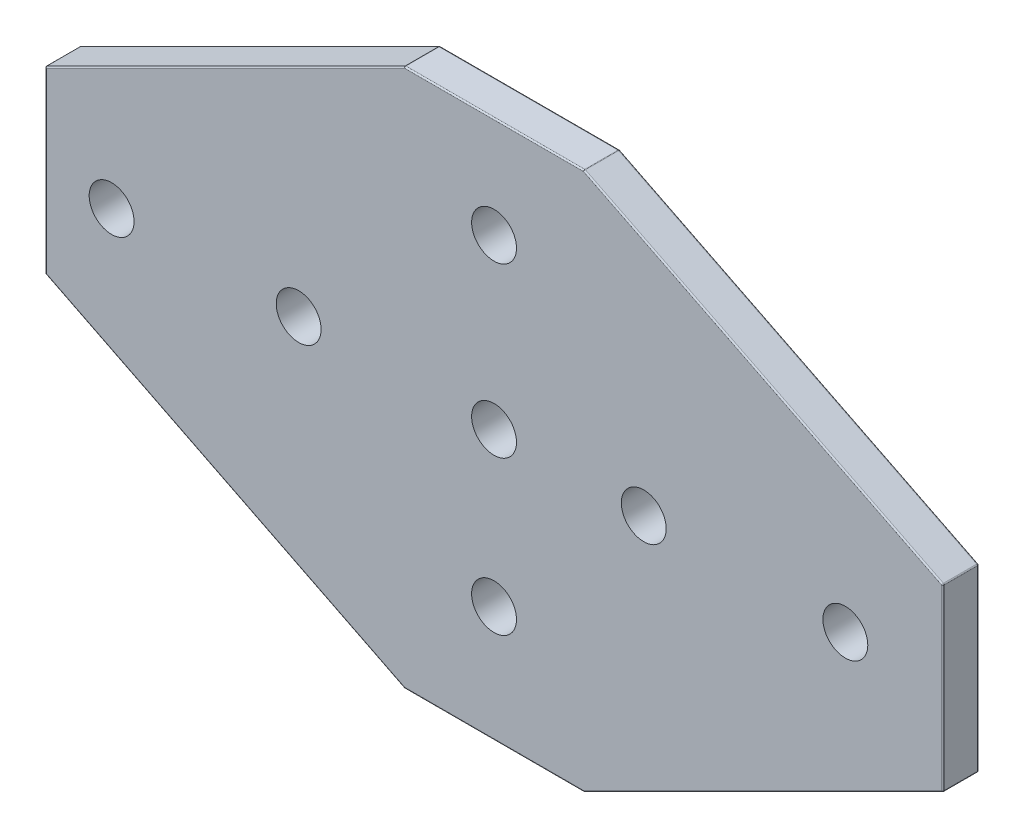
SolidWorks part; units mm, degrees
ref_plane "Front Plane" through (0, 0, 0) normal (0, 0, 1) x (1, 0, 0)
ref_plane "Top Plane" through (0, 0, 0) normal (0, 1, 0) x (1, 0, 0)
ref_plane "Right Plane" through (0, 0, 0) normal (1, 0, 0) x (0, 0, -1)
sketch "Sketch1" plane through (0, 0, 0) normal (0, 0, 1) x (1, 0, 0)
  line L0 (-50, 10) -> (-50, -10)
  line L1 (-50, 30) -> (50, 30) construction
  line L2 (-50, 30) -> (-50, -30) construction
  line L3 (-50, -30) -> (50, -30) construction
  line L4 (50, 30) -> (50, -30) construction
  line L5 (-10, 30) -> (10, 30)
  line L6 (50, 10) -> (50, -10)
  line L7 (-10, -30) -> (10, -30)
  line L8 (-50, 10) -> (-10, 30)
  line L9 (10, 30) -> (50, 10)
  line L10 (50, -10) -> (10, -30)
  line L11 (-50, -10) -> (-10, -30)
  line L12 (0, 30) -> (0, -30) construction
  line L13 (-50, 0) -> (50, 0) construction
  circle A0 centre (0, 0) radius 2.5 construction
  point P4 (-50, 0)
  point P6 (0, -30)
  point P15 (0, 30)
  point P16 (-50, 0)
  point P17 (50, 0)
  point P18 (0, -30)
  dimension "D4" = 5
  dimension "D1" = 100
  dimension "D2" = 60
  dimension "D3" = 20
extrude "Boss-Extrude2" add sketch "Sketch1" along normal blind 4
sketch "Sketch4" plane through (0, 0, 4) normal (0, 0, 1) x (1, 0, 0)
  line L8 (-10, 30) -> (-50, 10)
  line L9 (-50, 10) -> (-50, -10)
  line L10 (-50, -10) -> (-10, -30)
  line L11 (-10, -30) -> (10, -30)
  line L12 (10, -30) -> (50, -10)
  line L13 (50, -10) -> (50, 10)
  line L14 (50, 10) -> (10, 30)
  line L15 (10, 30) -> (-10, 30)
  line L16 (-10, 30) -> (-50, 10)
  line L17 (-50, 10) -> (-50, -10)
  line L18 (-50, -10) -> (-10, -30)
  line L19 (-10, -30) -> (10, -30)
  line L20 (10, -30) -> (50, -10)
  line L21 (50, -10) -> (50, 10)
  line L22 (50, 10) -> (10, 30)
  line L23 (10, 30) -> (-10, 30)
  circle A0 centre (0, 0) radius 2.5 construction
  circle A1 centre (0, 0) radius 2.5
  circle A2 centre (-21.7645, 0) radius 2.5
  circle A3 centre (-42.6028, 0) radius 2.5
  circle A4 centre (16.6764, 0) radius 2.5
  circle A5 centre (39.1347, 0) radius 2.5
  circle A6 centre (0, 18.7295) radius 2.5
  circle A7 centre (0, -17.1029) radius 2.5
  dimension "D1" = 0
extrude "Cut-Extrude4" cut sketch "Sketch4" against normal blind 4 flip side to cut
fillet "Fillet1" radius 0.15 24 edges at (-30, -20, 4) (-30, -20, 0) (0, 30, 4) (0, 30, 0) (30, 20, 4) (10, 30, 2) (30, 20, 0) (50, 0, 4) (50, 10, 2) (50, 0, 0) (30, -20, 4) (50, -10, 2) (30, -20, 0) (-10, -30, 2) (0, -30, 4) (10, -30, 2) (0, -30, 0) (-50, 0, 4) (-50, -10, 2) (-50, 0, 0) (-10, 30, 2) (-30, 20, 4) (-50, 10, 2) (-30, 20, 0)
